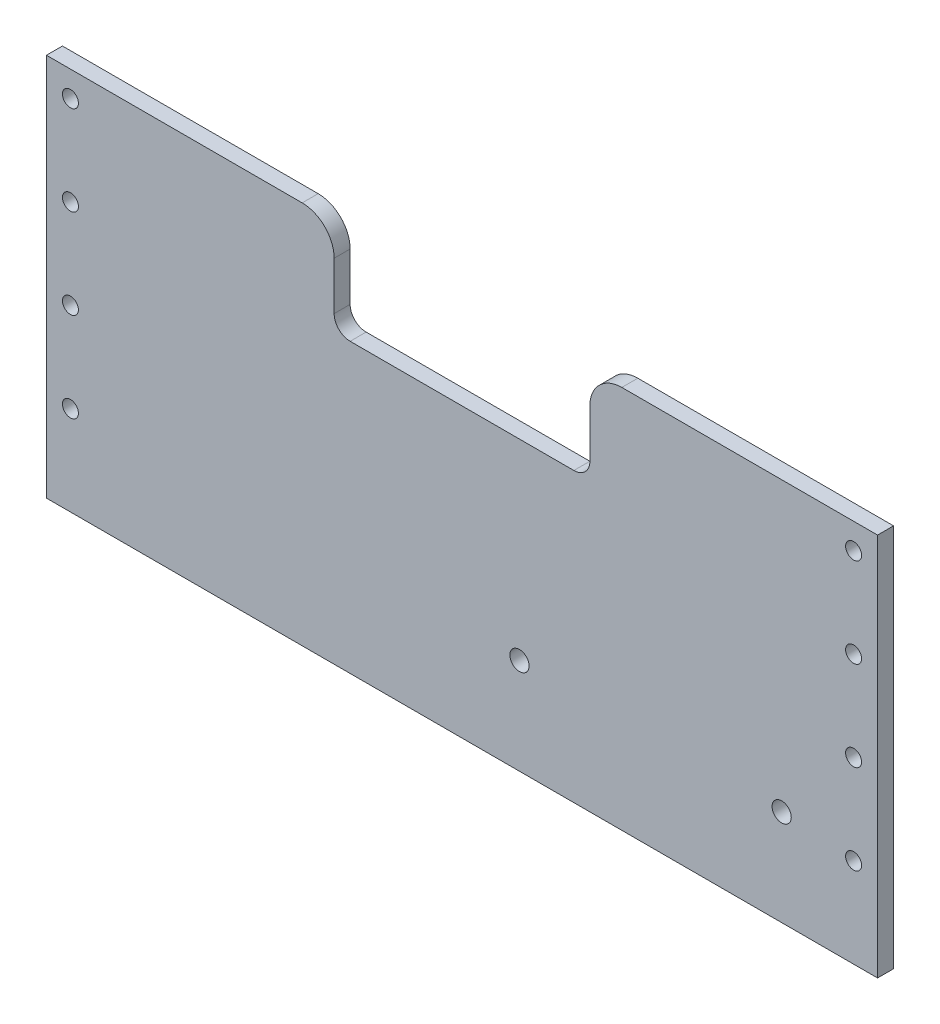
SolidWorks part; units mm, degrees
material "Hexcel AS4C (3000 Filaments)"
ref_plane "Front Plane" through (0, 0, 0) normal (0, 0, 1) x (1, 0, 0)
ref_plane "Top Plane" through (0, 0, 0) normal (0, 1, 0) x (1, 0, 0)
ref_plane "Right Plane" through (0, 0, 0) normal (1, 0, 0) x (0, 0, -1)
sketch "Sketch1" plane through (0, 0, 0) normal (0, 0, 1) x (1, 0, 0)
  line L0 (0, -58.42) -> (0, 58.42) construction
  line L2 (-82.55, 55.7897) -> (-82.55, -52.07)
  line L3 (-76.2, -58.42) -> (76.2, -58.42)
  line L4 (82.55, 55.7897) -> (82.55, -52.07)
  line L5 (-82.55, 58.42) -> (82.55, -58.42) construction
  line L6 (-82.55, -58.42) -> (82.55, 58.42) construction
  line L7 (-80.6901, 60.2799) -> (-75.4296, 65.5404)
  line L8 (-70.9395, 67.4003) -> (-50.8, 67.4003)
  line L9 (-46.3099, 65.5404) -> (-41.0494, 60.2799)
  line L10 (46.3099, 65.5404) -> (41.0494, 60.2799)
  line L11 (70.9395, 67.4003) -> (50.8, 67.4003)
  line L12 (80.6901, 60.2799) -> (75.4296, 65.5404)
  line L13 (-73.5697, 67.4003) -> (-82.55, 67.4003) construction
  line L14 (-82.55, 67.4003) -> (-82.55, 58.42) construction
  line L15 (-36.5592, 58.42) -> (0, 58.42)
  line L16 (0, 58.42) -> (36.5592, 58.42)
  circle A0 centre (-77.7875, -35.052) radius 1.5875
  circle A1 centre (-77.7875, -11.684) radius 1.5875
  circle A2 centre (-77.7875, 11.684) radius 1.5875
  circle A3 centre (-77.7875, 35.052) radius 1.5875
  circle A4 centre (77.7875, 35.052) radius 1.5875
  circle A5 centre (77.7875, 11.684) radius 1.5875
  circle A6 centre (77.7875, -11.684) radius 1.5875
  circle A7 centre (77.7875, -35.052) radius 1.5875
  arc A8 (82.55, 55.7897) -> (80.6901, 60.2799) centre (76.2, 55.7897) ccw
  arc A9 (75.4296, 65.5404) -> (70.9395, 67.4003) centre (70.9395, 61.0503) ccw
  arc A10 (46.3099, 65.5404) -> (50.8, 67.4003) centre (50.8, 61.0503) cw
  arc A11 (41.0494, 60.2799) -> (36.5592, 58.42) centre (36.5592, 64.77) cw
  arc A12 (-36.5592, 58.42) -> (-41.0494, 60.2799) centre (-36.5592, 64.77) cw
  arc A13 (-46.3099, 65.5404) -> (-50.8, 67.4003) centre (-50.8, 61.0503) ccw
  arc A14 (-70.9395, 67.4003) -> (-75.4296, 65.5404) centre (-70.9395, 61.0503) ccw
  arc A15 (-82.55, 55.7897) -> (-80.6901, 60.2799) centre (-76.2, 55.7897) cw
  arc A16 (76.2, -58.42) -> (82.55, -52.07) centre (76.2, -52.07) ccw
  arc A17 (-76.2, -58.42) -> (-82.55, -52.07) centre (-76.2, -52.07) cw
  circle A18 centre (-70.9395, 61.0503) radius 1.5875
  circle A19 centre (-50.8, 61.0503) radius 1.5875
  circle A20 centre (50.8, 61.0503) radius 1.5875
  circle A21 centre (70.9395, 61.0503) radius 1.5875
  point P0 (0, 0)
  point P36 (73.5697, 67.4003)
  point P39 (48.1697, 67.4003)
  point P42 (39.1895, 58.42)
  point P45 (-39.1895, 58.42)
  point P48 (-48.1697, 67.4003)
  dimension "D3" = 3.175
  dimension "D11" = 6.35
  dimension "D12" = 6.35
  dimension "D13" = 3.175
  dimension "D14" = 3.175
  dimension "D1" = 165.1
  dimension "D2" = 116.84
  dimension "D4" = 23.368
  dimension "D5" = 4.7625
  dimension "D7" = 46.736
  dimension "D8" = 12.7
  dimension "D9" = 135
  dimension "D10" = 25.4
  dimension "D6" = 4
extrude "Boss-Extrude1" [suppressed] add sketch "Sketch1" along normal blind 1.5
sketch "Sketch2" [suppressed] plane through (0, 0, 1.5) normal (0, 0, 1) x (1, 0, 0)
  line L0 (0, -45.72) -> (0, 6.3634) construction
  line L1 (0, -58.42) -> (0, 63.5) construction
  line L3 (-82.55, 1.8599) -> (82.55, 1.8599) construction
  line L4 (-82.55, 55.7897) -> (-82.55, -52.07) construction
  line L5 (82.55, -52.07) -> (82.55, 55.7897) construction
  line L7 (-76.2, -58.42) -> (76.2, -58.42) construction
  circle A0 centre (0, -45.72) radius 1.9062
  circle A1 centre (0, 6.3634) radius 1.9062
  dimension "D2" = 3.8125
  dimension "D3" = 3.8125
  dimension "D1" = 52.0834
  dimension "D4" = 12.7
extrude "Cut-Extrude1" [suppressed] cut sketch "Sketch2" against normal through all
sketch "Sketch3" [suppressed] plane through (0, 0, 1.5) normal (0, 0, 1) x (1, 0, 0)
  line L0 (0, 50.8) -> (0, 30.8) construction
  line L1 (-10, 40.8) -> (10, 40.8) construction
  line L2 (-10, 40.8) -> (0, 50.8) construction
  line L3 (0, 50.8) -> (10, 40.8) construction
  line L4 (10, 40.8) -> (0, 30.8) construction
  line L5 (0, 30.8) -> (-10, 40.8) construction
  line L6 (0, 63.5) -> (0, -58.42) construction
  line L8 (-76.2, -58.42) -> (76.2, -58.42) construction
  circle A0 centre (0, 50.8) radius 1.8669
  circle A1 centre (-10, 40.8) radius 1.8669
  circle A2 centre (0, 30.8) radius 1.8669
  circle A3 centre (10, 40.8) radius 1.8669
  dimension "D1" = 3.7338
  dimension "D2" = 12.7
extrude "Cut-Extrude2" [suppressed] cut sketch "Sketch3" against normal through all
sketch "Sketch4" [suppressed] plane through (0, 0, 1.5) normal (0, 0, 1) x (1, 0, 0)
  line L0 (0, 58.42) -> (0, -58.42) construction
  line L1 (36.5592, 58.42) -> (-36.5592, 58.42) construction
  line L2 (-76.2, -58.42) -> (76.2, -58.42) construction
  line L5 (0, 33.045) -> (0, 52.045) construction
  line L6 (-9.5, 42.545) -> (9.5, 42.545) construction
  circle A14 centre (0, 42.545) radius 8 construction
  circle A15 centre (0, 42.545) radius 9.5 construction
  circle A16 centre (0, 50.545) radius 1.5
  circle A17 centre (0, 34.545) radius 1.5
  circle A18 centre (-9.5, 42.545) radius 1.5
  circle A19 centre (9.5, 42.545) radius 1.5
  dimension "D1" = 15.875
  dimension "D3" = 16
  dimension "D4" = 19
  dimension "D5" = 3
  dimension "D6" = 3
  dimension "D7" = 3
  dimension "D8" = 3
extrude "Cut-Extrude3" [suppressed] cut sketch "Sketch4" against normal through all
sketch "Sketch5" plane through (0, 0, 0) normal (0, 0, 1) x (1, 0, 0)
  line L0 (0, -58.337) -> (0, 30.563) construction
  line L1 (-43.2483, 30.563) -> (43.2483, 30.563) construction
  line L2 (-82.55, 17.863) -> (-82.55, -58.337)
  line L3 (-82.55, -58.337) -> (82.55, -58.337)
  line L4 (82.55, 17.863) -> (82.55, -58.337)
  line L5 (-43.2483, 30.563) -> (82.55, -58.337) construction
  line L6 (-82.55, -58.337) -> (43.2483, 30.563) construction
  line L7 (-77.7875, -58.337) -> (-77.7875, 30.563) construction
  line L8 (-77.7875, -40.557) -> (-77.7875, -22.777) construction
  line L9 (77.7875, -58.337) -> (77.7875, 30.563) construction
  line L11 (11.4166, -39.287) -> (63.5, -39.287) construction
  line L13 (-82.55, -0.6801) -> (82.55, -0.6801) construction
  line L14 (-82.55, 17.863) -> (-31.75, 17.863)
  line L15 (-22.225, -1.187) -> (22.225, -1.187)
  line L16 (-25.4, 1.988) -> (-25.4, 11.513)
  line L17 (25.4, 1.988) -> (25.4, 11.513)
  line L18 (31.75, 17.863) -> (82.55, 17.863)
  circle A0 centre (-77.7875, -40.557) radius 1.5875
  circle A1 centre (-77.7875, -22.777) radius 1.5875
  circle A2 centre (-77.7875, -4.997) radius 1.5875
  circle A3 centre (-77.7875, 12.783) radius 1.5875
  circle A8 centre (11.4166, -39.287) radius 1.9062
  circle A9 centre (63.5, -39.287) radius 1.9062
  circle A10 centre (21.1667, -9.332) radius 1.5875 construction
  circle A11 centre (-21.1667, -9.332) radius 1.5875 construction
  arc A12 (-25.4, 11.513) -> (-31.75, 17.863) centre (-31.75, 11.513) ccw
  arc A13 (25.4, 11.513) -> (31.75, 17.863) centre (31.75, 11.513) cw
  arc A14 (25.4, 1.988) -> (22.225, -1.187) centre (22.225, 1.988) cw
  arc A15 (-25.4, 1.988) -> (-22.225, -1.187) centre (-22.225, 1.988) ccw
  circle A16 centre (77.7875, 12.783) radius 1.5875
  circle A17 centre (77.7875, -4.997) radius 1.5875
  circle A18 centre (77.7875, -22.777) radius 1.5875
  circle A19 centre (77.7875, -40.557) radius 1.5875
  point P0 (0, 0)
  point P52 (25.4, 17.863)
  point P55 (25.4, -1.187)
  point P58 (-25.4, -1.187)
  point P59 (0, -1.187)
  dimension "D13" = 3.175
  dimension "D6" = 4
  dimension "D4" = 3.175
  dimension "D12" = 3.175
  dimension "D17" = 6.35
  dimension "D18" = 6.35
  dimension "D19" = 3.175
  dimension "D20" = 3.175
  dimension "D22" = 3.8125
  dimension "D23" = 3.8125
  dimension "D2" = 165.1
  dimension "D3" = 4.7625
  dimension "D5" = 17.78
  dimension "D7" = 17.78
  dimension "D8" = 39.895
  dimension "D9" = 39.895
  dimension "D10" = 61.3833
  dimension "D11" = 61.3833
  dimension "D14" = 12.7
  dimension "D15" = 50.8
  dimension "D16" = 19.05
  dimension "D21" = 52.0834
  dimension "D25" = 88.9
  dimension "D24" = 19.05
  dimension "D26" = 19.05
extrude "Boss-Extrude2" add sketch "Sketch5" along normal blind 3.175
equation "\"Top Plate Width\" = 4.5in"
equation "\"Plate Width\" = 3.5in"
equation "\"Plate Thickness\" = 0.375in"
equation "\"Num holes\" = 4"
equation "\"Plate Height\" = 1.25in"
equation "\"Plate Clearance Hole Diameter\" = 0.125in"
equation "\"D3@Sketch1\"=\"Plate Clearance Hole Diameter\""
equation "\"Hole Spacing\"= \"Plate Width\" / ( \"Num holes\" + 1 )"
equation "\"Plate Tap Hole Diameter\" = 0.116in"
equation "\"Bottom Plate Length\" = 6.5in"
equation "\"D2@Sketch5\"=\"Bottom Plate Length\""
equation "\"D3@Sketch5\"=\"Plate Thickness\"/2"
equation "\"D4@Sketch5\"=\"Plate Clearance Hole Diameter\""
equation "\"D5@Sketch5\"=(\"Plate Width\" )/ ( \"Num holes\" + 1 )"
equation "\"D6@Sketch5\"=\"Num holes\""
equation "\"D7@Sketch5\"=\"Plate Width\"/ ( \"Num holes\" + 1 )"
equation "\"D12@Sketch5\"=\"Plate Clearance Hole Diameter\""
equation "\"D13@Sketch5\"=\"Plate Clearance Hole Diameter\""
equation "\"D25@Sketch5\"=\"Plate Width\""
